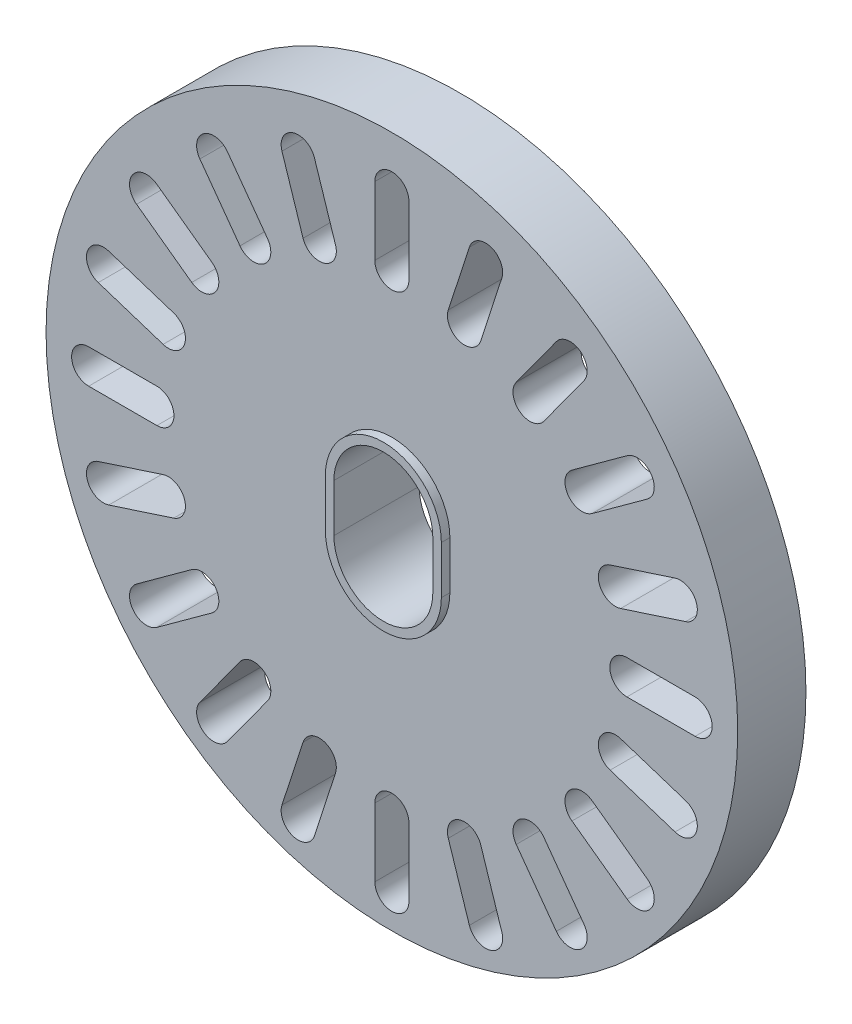
SolidWorks part; units mm, degrees
ref_plane "Front Plane" through (0, 0, 0) normal (0, 0, 1) x (1, 0, 0)
ref_plane "Top Plane" through (0, 0, 0) normal (0, 1, 0) x (1, 0, 0)
ref_plane "Right Plane" through (0, 0, 0) normal (1, 0, 0) x (0, 0, -1)
sketch "Sketch1" plane through (0, 0, 0) normal (0, 0, 1) x (1, 0, 0)
  line L0 (0, 0.889) -> (0, -0.889) construction
  line L1 (1.8415, 0.889) -> (1.8415, -0.889)
  line L2 (-1.8415, 0.889) -> (-1.8415, -0.889)
  line L3 (0, 0) -> (0, 12.8778) construction
  line L4 (0, 10.9728) -> (0, 8.4328) construction
  line L5 (0.635, 10.9728) -> (0.635, 8.4328)
  line L6 (-0.635, 10.9728) -> (-0.635, 8.4328)
  line L7 (3.4889, 10.4202) -> (2.704, 8.0045) construction
  line L8 (4.0928, 10.224) -> (3.3079, 7.8083)
  line L9 (2.885, 10.6164) -> (2.1001, 8.2008)
  line L10 (6.6363, 8.8165) -> (5.1433, 6.7616) construction
  line L11 (7.15, 8.4433) -> (5.657, 6.3884)
  line L12 (6.1225, 9.1898) -> (4.6296, 7.1349)
  line L13 (9.134, 6.3188) -> (7.0791, 4.8258) construction
  line L14 (9.5073, 5.805) -> (7.4524, 4.3121)
  line L15 (8.7608, 6.8325) -> (6.7059, 5.3395)
  line L16 (10.7377, 3.1714) -> (8.322, 2.3865) construction
  line L17 (10.9339, 2.5675) -> (8.5183, 1.7826)
  line L18 (10.5415, 3.7753) -> (8.1258, 2.9904)
  line L19 (11.2903, -0.3175) -> (8.7503, -0.3175) construction
  line L20 (11.2903, -0.9525) -> (8.7503, -0.9525)
  line L21 (11.2903, 0.3175) -> (8.7503, 0.3175)
  line L22 (10.7377, -3.8064) -> (8.322, -3.0215) construction
  line L23 (10.5415, -4.4103) -> (8.1258, -3.6254)
  line L24 (10.9339, -3.2025) -> (8.5183, -2.4176)
  line L25 (9.134, -6.9538) -> (7.0791, -5.4608) construction
  line L26 (8.7608, -7.4675) -> (6.7059, -5.9745)
  line L27 (9.5073, -6.44) -> (7.4524, -4.9471)
  line L28 (6.6363, -9.4515) -> (5.1433, -7.3966) construction
  line L29 (6.1225, -9.8248) -> (4.6296, -7.7699)
  line L30 (7.15, -9.0783) -> (5.657, -7.0234)
  line L31 (3.4889, -11.0552) -> (2.704, -8.6395) construction
  line L32 (2.885, -11.2514) -> (2.1001, -8.8358)
  line L33 (4.0928, -10.859) -> (3.3079, -8.4433)
  line L34 (0, -11.6078) -> (0, -9.0678) construction
  line L35 (-0.635, -11.6078) -> (-0.635, -9.0678)
  line L36 (0.635, -11.6078) -> (0.635, -9.0678)
  line L37 (-3.4889, -11.0552) -> (-2.704, -8.6395) construction
  line L38 (-4.0928, -10.859) -> (-3.3079, -8.4433)
  line L39 (-2.885, -11.2514) -> (-2.1001, -8.8358)
  line L40 (-6.6363, -9.4515) -> (-5.1433, -7.3966) construction
  line L41 (-7.15, -9.0783) -> (-5.657, -7.0234)
  line L42 (-6.1225, -9.8248) -> (-4.6296, -7.7699)
  line L43 (-9.134, -6.9538) -> (-7.0791, -5.4608) construction
  line L44 (-9.5073, -6.44) -> (-7.4524, -4.9471)
  line L45 (-8.7608, -7.4675) -> (-6.7059, -5.9745)
  line L46 (-10.7377, -3.8064) -> (-8.322, -3.0215) construction
  line L47 (-10.9339, -3.2025) -> (-8.5183, -2.4176)
  line L48 (-10.5415, -4.4103) -> (-8.1258, -3.6254)
  line L49 (-11.2903, -0.3175) -> (-8.7503, -0.3175) construction
  line L50 (-11.2903, 0.3175) -> (-8.7503, 0.3175)
  line L51 (-11.2903, -0.9525) -> (-8.7503, -0.9525)
  line L52 (-10.7377, 3.1714) -> (-8.322, 2.3865) construction
  line L53 (-10.5415, 3.7753) -> (-8.1258, 2.9904)
  line L54 (-10.9339, 2.5675) -> (-8.5183, 1.7826)
  line L55 (-9.134, 6.3188) -> (-7.0791, 4.8258) construction
  line L56 (-8.7608, 6.8325) -> (-6.7059, 5.3395)
  line L57 (-9.5073, 5.805) -> (-7.4524, 4.3121)
  line L58 (-6.6363, 8.8165) -> (-5.1433, 6.7616) construction
  line L59 (-6.1225, 9.1898) -> (-4.6296, 7.1349)
  line L60 (-7.15, 8.4433) -> (-5.657, 6.3884)
  line L61 (-3.4889, 10.4202) -> (-2.704, 8.0045) construction
  line L62 (-2.885, 10.6164) -> (-2.1001, 8.2008)
  line L63 (-4.0928, 10.224) -> (-3.3079, 7.8083)
  circle A0 centre (0, 0) radius 12.8778
  arc A1 (1.8415, 0.889) -> (-1.8415, 0.889) centre (0, 0.889) ccw
  arc A2 (-1.8415, -0.889) -> (1.8415, -0.889) centre (0, -0.889) ccw
  arc A3 (0.635, 10.9728) -> (-0.635, 10.9728) centre (0, 10.9728) ccw
  arc A4 (-0.635, 8.4328) -> (0.635, 8.4328) centre (0, 8.4328) ccw
  arc A5 (4.0928, 10.224) -> (2.885, 10.6164) centre (3.4889, 10.4202) ccw
  arc A6 (2.1001, 8.2008) -> (3.3079, 7.8083) centre (2.704, 8.0045) ccw
  arc A7 (7.15, 8.4433) -> (6.1225, 9.1898) centre (6.6363, 8.8165) ccw
  arc A8 (4.6296, 7.1349) -> (5.657, 6.3884) centre (5.1433, 6.7616) ccw
  arc A9 (9.5073, 5.805) -> (8.7608, 6.8325) centre (9.134, 6.3188) ccw
  arc A10 (6.7059, 5.3395) -> (7.4524, 4.3121) centre (7.0791, 4.8258) ccw
  arc A11 (10.9339, 2.5675) -> (10.5415, 3.7753) centre (10.7377, 3.1714) ccw
  arc A12 (8.1258, 2.9904) -> (8.5183, 1.7826) centre (8.322, 2.3865) ccw
  arc A13 (11.2903, -0.9525) -> (11.2903, 0.3175) centre (11.2903, -0.3175) ccw
  arc A14 (8.7503, 0.3175) -> (8.7503, -0.9525) centre (8.7503, -0.3175) ccw
  arc A15 (10.5415, -4.4103) -> (10.9339, -3.2025) centre (10.7377, -3.8064) ccw
  arc A16 (8.5183, -2.4176) -> (8.1258, -3.6254) centre (8.322, -3.0215) ccw
  arc A17 (8.7608, -7.4675) -> (9.5073, -6.44) centre (9.134, -6.9538) ccw
  arc A18 (7.4524, -4.9471) -> (6.7059, -5.9745) centre (7.0791, -5.4608) ccw
  arc A19 (6.1225, -9.8248) -> (7.15, -9.0783) centre (6.6363, -9.4515) ccw
  arc A20 (5.657, -7.0234) -> (4.6296, -7.7699) centre (5.1433, -7.3966) ccw
  arc A21 (2.885, -11.2514) -> (4.0928, -10.859) centre (3.4889, -11.0552) ccw
  arc A22 (3.3079, -8.4433) -> (2.1001, -8.8358) centre (2.704, -8.6395) ccw
  arc A23 (-0.635, -11.6078) -> (0.635, -11.6078) centre (0, -11.6078) ccw
  arc A24 (0.635, -9.0678) -> (-0.635, -9.0678) centre (0, -9.0678) ccw
  arc A25 (-4.0928, -10.859) -> (-2.885, -11.2514) centre (-3.4889, -11.0552) ccw
  arc A26 (-2.1001, -8.8358) -> (-3.3079, -8.4433) centre (-2.704, -8.6395) ccw
  arc A27 (-7.15, -9.0783) -> (-6.1225, -9.8248) centre (-6.6363, -9.4515) ccw
  arc A28 (-4.6296, -7.7699) -> (-5.657, -7.0234) centre (-5.1433, -7.3966) ccw
  arc A29 (-9.5073, -6.44) -> (-8.7608, -7.4675) centre (-9.134, -6.9538) ccw
  arc A30 (-6.7059, -5.9745) -> (-7.4524, -4.9471) centre (-7.0791, -5.4608) ccw
  arc A31 (-10.9339, -3.2025) -> (-10.5415, -4.4103) centre (-10.7377, -3.8064) ccw
  arc A32 (-8.1258, -3.6254) -> (-8.5183, -2.4176) centre (-8.322, -3.0215) ccw
  arc A33 (-11.2903, 0.3175) -> (-11.2903, -0.9525) centre (-11.2903, -0.3175) ccw
  arc A34 (-8.7503, -0.9525) -> (-8.7503, 0.3175) centre (-8.7503, -0.3175) ccw
  arc A35 (-10.5415, 3.7753) -> (-10.9339, 2.5675) centre (-10.7377, 3.1714) ccw
  arc A36 (-8.5183, 1.7826) -> (-8.1258, 2.9904) centre (-8.322, 2.3865) ccw
  arc A37 (-8.7608, 6.8325) -> (-9.5073, 5.805) centre (-9.134, 6.3188) ccw
  arc A38 (-7.4524, 4.3121) -> (-6.7059, 5.3395) centre (-7.0791, 4.8258) ccw
  arc A39 (-6.1225, 9.1898) -> (-7.15, 8.4433) centre (-6.6363, 8.8165) ccw
  arc A40 (-5.657, 6.3884) -> (-4.6296, 7.1349) centre (-5.1433, 6.7616) ccw
  arc A41 (-2.885, 10.6164) -> (-4.0928, 10.224) centre (-3.4889, 10.4202) ccw
  arc A42 (-3.3079, 7.8083) -> (-2.1001, 8.2008) centre (-2.704, 8.0045) ccw
  point P5 (0, 0)
  point P10 (0, 2.7305)
  point P11 (0, -2.7305)
  point P15 (0, 9.7028)
  point P20 (0, 11.6078)
  point P21 (0, 7.7978)
  point P27 (3.0964, 9.2124)
  point P34 (5.8898, 7.7891)
  point P41 (8.1066, 5.5723)
  point P48 (9.5299, 2.7789)
  point P55 (10.0203, -0.3175)
  point P62 (9.5299, -3.4139)
  point P69 (8.1066, -6.2073)
  point P76 (5.8898, -8.4241)
  point P83 (3.0964, -9.8474)
  point P90 (0, -10.3378)
  point P97 (-3.0964, -9.8474)
  point P104 (-5.8898, -8.4241)
  point P111 (-8.1066, -6.2073)
  point P118 (-9.5299, -3.4139)
  point P125 (-10.0203, -0.3175)
  point P132 (-9.5299, 2.7789)
  point P139 (-8.1066, 5.5723)
  point P146 (-5.8898, 7.7891)
  point P153 (-3.0964, 9.2124)
  point P158 (0, -0.3175)
  dimension "D1" = 25.7556
  dimension "D2" = 3.683
  dimension "D3" = 5.461
  dimension "D4" = 3.81
  dimension "D5" = 1.27
  dimension "D6" = 1.27
  dimension "D7" = 20
extrude "Boss-Extrude1" add sketch "Sketch1" along normal blind 2.54
sketch "Sketch2" plane through (0, 0, 2.54) normal (0, 0, 1) x (1, 0, 0)
  line L0 (1.8415, -0.889) -> (1.8415, 0.889) construction
  line L1 (-1.8415, 0.889) -> (-1.8415, -0.889) construction
  line L2 (1.8415, -0.889) -> (1.8415, 0.889)
  line L3 (-1.8415, 0.889) -> (-1.8415, -0.889)
  line L4 (-2.159, 0.889) -> (-2.159, -0.889)
  line L5 (2.159, -0.889) -> (2.159, 0.889)
  arc A0 (-1.8415, -0.889) -> (1.8415, -0.889) centre (0, -0.889) ccw construction
  arc A1 (1.8415, 0.889) -> (-1.8415, 0.889) centre (0, 0.889) ccw construction
  arc A2 (-1.8415, -0.889) -> (1.8415, -0.889) centre (0, -0.889) ccw
  arc A3 (1.8415, 0.889) -> (-1.8415, 0.889) centre (0, 0.889) ccw
  arc A4 (2.159, 0.889) -> (-2.159, 0.889) centre (0, 0.889) ccw
  arc A5 (-2.159, -0.889) -> (2.159, -0.889) centre (0, -0.889) ccw
  dimension "D1" = 0.3175
extrude "Boss-Extrude2" add sketch "Sketch2" along normal blind 0.3175
ref_plane "Plane1" through (0, 0, 1.27) normal (0, 0, 1) x (1, 0, 0)
mirror "Mirror1" about plane through (0, 0, 1.27) normal (0, 0, 1) of "Boss-Extrude2"
